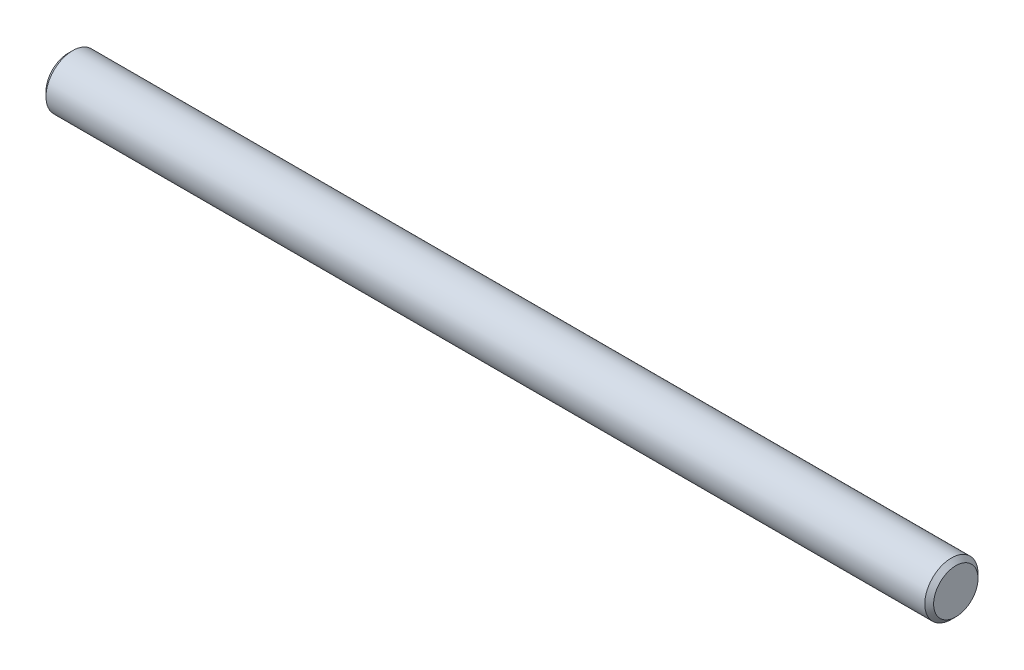
SolidWorks part; units mm, degrees
ref_plane "Front Plane" through (0, 0, 0) normal (0, 0, 1) x (1, 0, 0)
ref_plane "Top Plane" through (0, 0, 0) normal (0, 1, 0) x (1, 0, 0)
ref_plane "Right Plane" through (0, 0, 0) normal (1, 0, 0) x (0, 0, -1)
sketch "Sketch1" plane through (0, 0, 0) normal (1, 0, 0) x (0, 0, -1)
  circle A0 centre (0, 0) radius 3
  dimension "D1" = 6
extrude "Boss-Extrude1" add sketch "Sketch1" along normal mid plane 100
chamfer "Chamfer1" distance 0.5 angle 45 2 edges at (50, 0, -3) (-50, 0, -3)
equation "\"diameter\"=6"
equation "\"D1@Sketch1\"=\"diameter\""
equation "\"length\"=100"
equation "\"D1@Boss-Extrude1\"=\"length\""
